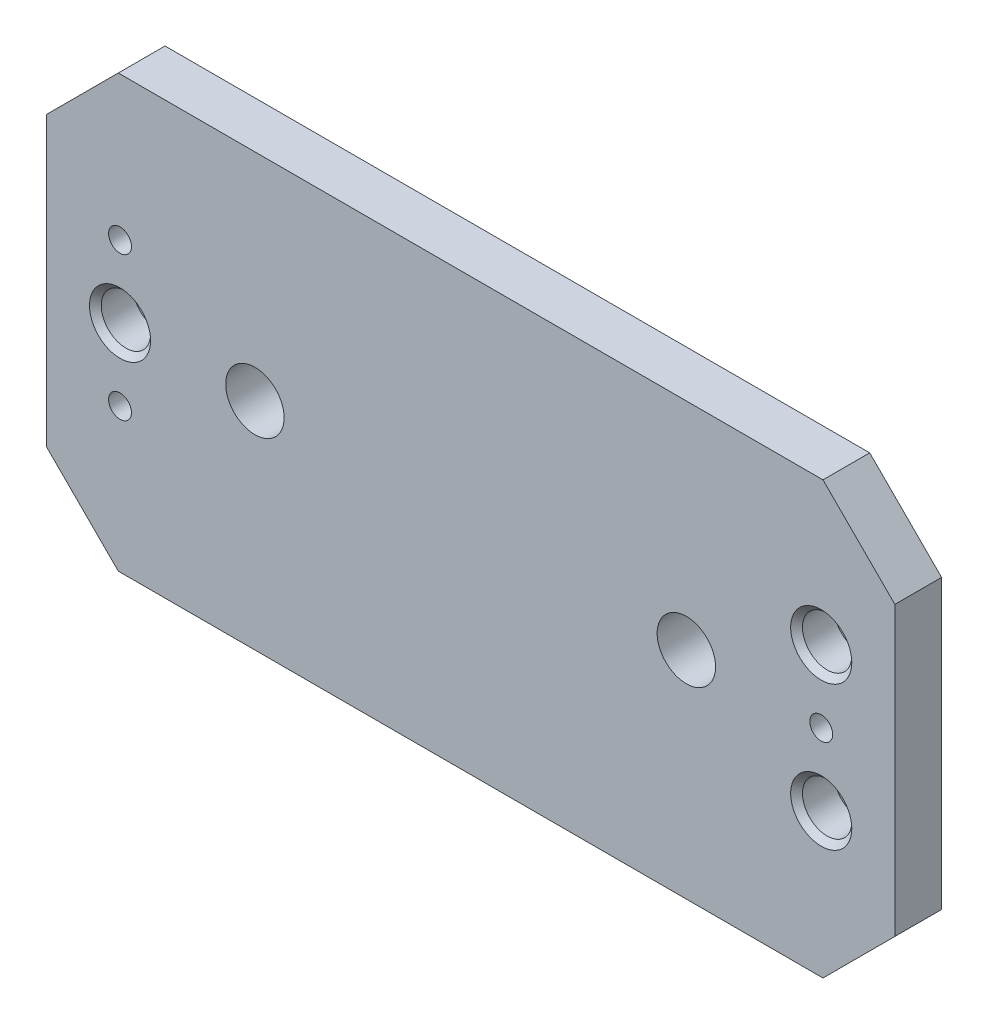
SolidWorks part; units mm, degrees
material "6061-T6 Al"
ref_plane "Front Plane" through (0, 0, 0) normal (0, 0, 1) x (1, 0, 0)
ref_plane "Top Plane" through (0, 0, 0) normal (0, 1, 0) x (1, 0, 0)
ref_plane "Right Plane" through (0, 0, 0) normal (1, 0, 0) x (0, 0, -1)
sketch "Sketch1" plane through (0, 0, 0) normal (0, 0, 1) x (1, 0, 0)
  line L0 (0, 0) -> (0, -38.1) construction
  line L1 (74.93, -38.1) -> (-74.93, -38.1)
  line L2 (74.93, -38.1) -> (74.93, 38.1)
  line L3 (74.93, 38.1) -> (-74.93, 38.1)
  line L4 (-74.93, -38.1) -> (-74.93, 38.1)
  line L5 (0, 0) -> (-74.93, 0) construction
  dimension "D1" = 149.86
  dimension "D2" = 76.2
extrude "Extrude1" add sketch "Sketch1" along normal blind 9.017
sketch "Sketch2" plane through (0, 0, 0) normal (0, 0, -1) x (-1, 0, 0)
  line L0 (-74.93, 38.1) -> (74.93, 38.1) construction
  line L1 (-74.93, -38.1) -> (74.93, -38.1)
  line L2 (-74.93, -38.1) -> (-74.93, 38.1)
  line L3 (-74.93, 38.1) -> (74.93, 38.1)
  line L4 (74.93, -38.1) -> (74.93, 38.1)
  line L5 (74.93, -38.1) -> (-74.93, -38.1) construction
  line L6 (-74.93, -38.1) -> (-74.93, 38.1) construction
  line L7 (74.93, 38.1) -> (74.93, -38.1) construction
  line L8 (0, 0) -> (-52.4002, 0) construction
  line L9 (-71.4502, -19.05) -> (-52.4002, -19.05)
  line L10 (-71.4502, -19.05) -> (-71.4502, 19.05)
  line L11 (-71.4502, 19.05) -> (-52.4002, 19.05)
  line L12 (-52.4002, -19.05) -> (-52.4002, 19.05)
  line L13 (52.4002, -19.05) -> (71.4502, -19.05)
  line L14 (52.4002, -19.05) -> (52.4002, 19.05)
  line L15 (52.4002, 19.05) -> (71.4502, 19.05)
  line L16 (71.4502, -19.05) -> (71.4502, 19.05)
  line L17 (0, 0) -> (52.4002, 0) construction
  dimension "D1" = 19.05
  dimension "D2" = 52.4002
  dimension "D3" = 38.1
extrude "Cut-Extrude1" cut sketch "Sketch2" against normal blind 0.762
hole_wizard "#10-32 Tapped Hole1" positions "Sketch4" profile "Sketch3" tap size "#10-32" standard "Ansi Inch" end condition through all
sketch "Sketch4" plane through (0, 0, 9.017) normal (0, 0, 1) x (1, 0, 0)
  line L1 (-61.9252, -12.7) -> (-61.9252, 12.7) construction
  line L2 (0, 0) -> (61.9252, 0) construction
  point P0 (61.9252, 0)
  point P1 (-61.9252, -12.7)
  point P9 (-61.9252, 12.7)
  dimension "D2" = 12.7
  dimension "D3" = 61.9252
  dimension "D4" = 61.9252
  dimension "D5" = 25.4
sketch "Sketch3" plane through (61.9252, 0, 9.017) normal (1, 0, 0) x (0, -1, 0)
  line L0 (0, 0) -> (0, 9.017)
  line L1 (0, 9.017) -> (2.0193, 9.017)
  line L2 (2.0193, 9.017) -> (2.0193, 0)
  line L5 (2.0193, 0) -> (0, 0)
  line L11 (0, -6.35) -> (0, 107.95) construction
  dimension "Thru Tap Drill Dia." = 4.0386
  dimension "Thru Tap Drill Depth" = 9.017
cosmetic thread "Hole Thread1" parameters "D2"=4.826
cosmetic thread "Hole Thread2" parameters "D2"=4.826
cosmetic thread "Hole Thread3" parameters "D2"=4.826
hole_wizard "CBORE for #10 Socket Head Cap Screw1" positions "Sketch6" profile "Sketch5" counterbore size "#10" standard "Ansi Inch" end condition through all
sketch "Sketch6" plane through (0, 0, 9.017) normal (0, 0, 1) x (1, 0, 0)
  line L0 (61.9252, 0) -> (61.9252, -12.7) construction
  line L2 (0, 0) -> (-61.9252, 0) construction
  line L3 (61.9252, -12.7) -> (61.9252, 12.7) construction
  point P0 (61.9252, -12.7)
  point P1 (-61.9252, 0)
  point P10 (61.9252, 12.7)
  dimension "D1" = 12.7
  dimension "D2" = 61.9252
  dimension "D3" = 25.4
sketch "Sketch5" plane through (61.9252, -12.7, 9.017) normal (1, 0, 0) x (0, -1, 0)
  line L0 (0, 0) -> (0, 9.017)
  line L1 (0, 9.017) -> (2.8067, 9.017)
  line L3 (2.8067, 9.017) -> (2.8067, 6.6548)
  line L4 (4.3561, 6.6548) -> (2.8067, 6.6548)
  line L5 (4.3561, 6.6548) -> (4.3561, 1.0414)
  line L6 (4.3561, 1.0414) -> (5.3975, 0)
  line L7 (5.3975, 0) -> (0, 0)
  line L8 (-4.3561, 1.0414) -> (-5.3975, 0) construction
  line L11 (0, -6.35) -> (0, 107.95) construction
  dimension "Thru Hole Dia." = 5.6134
  dimension "Thru Hole Depth" = 9.017
  dimension "C'Bore Dia." = 8.7122
  dimension "C'Bore Depth" = 6.6548
  dimension "Near C'Sink Dia." = 10.795
  dimension "Near C'Sink Angle" = 90
chamfer "Chamfer1" distance 12.7 angle 45 4 edges at (-74.93, -38.1, 4.8895) (-74.93, 38.1, 4.8895) (74.93, -38.1, 4.8895) (74.93, 38.1, 4.8895)
sketch "Sketch7" plane through (0, 0, 0) normal (0, 0, -1) x (-1, 0, 0)
  line L0 (61.9252, -12.7) -> (61.9252, -19.05) construction
  line L1 (62.7126, -19.05) -> (61.1378, -19.05)
  line L2 (62.7126, -19.05) -> (62.7126, 19.05)
  line L3 (62.7126, 19.05) -> (61.1378, 19.05)
  line L4 (61.1378, -19.05) -> (61.1378, 19.05)
  line L5 (-61.1378, -19.05) -> (-62.7126, -19.05)
  line L6 (-61.1378, -19.05) -> (-61.1378, 19.05)
  line L7 (-61.1378, 19.05) -> (-62.7126, 19.05)
  line L8 (-62.7126, -19.05) -> (-62.7126, 19.05)
  line L9 (-61.9252, -12.7) -> (-61.9252, -19.05) construction
  line L10 (52.4002, -19.05) -> (71.4502, -19.05) construction
  line L11 (71.4502, 19.05) -> (52.4002, 19.05) construction
  line L12 (-71.4502, -19.05) -> (-52.4002, -19.05) construction
  line L13 (-52.4002, 19.05) -> (-71.4502, 19.05) construction
  dimension "D1" = 1.5748
extrude "Cut-Extrude2" cut sketch "Sketch7" against normal up to surface (0.762 mm away) up to face at (-61.9252, 0, 0.762)
hole_wizard "13/32 (0.40625) Diameter Hole1" positions "Sketch9" profile "Sketch8" hole size "13/32" standard "Ansi Inch" end condition through all
sketch "Sketch9" plane through (0, 0, 9.017) normal (0, 0, 1) x (1, 0, 0)
  line L0 (-61.9252, 0) -> (-38.1, 0) construction
  line L1 (61.9252, 0) -> (38.1, 0) construction
  point P0 (38.1, 0)
  point P1 (-38.1, 0)
  dimension "D1" = 38.1
  dimension "D2" = 38.1
sketch "Sketch8" plane through (38.1, 0, 9.017) normal (1, 0, 0) x (0, -1, 0)
  line L0 (0, 0) -> (0, 9.017)
  line L1 (0, 9.017) -> (5.1594, 9.017)
  line L2 (5.1594, 9.017) -> (5.1594, 0)
  line L5 (5.1594, 0) -> (0, 0)
  line L11 (0, -6.35) -> (0, 107.95) construction
  dimension "Thru Hole Dia." = 10.3187
  dimension "Thru Hole Depth" = 9.017
